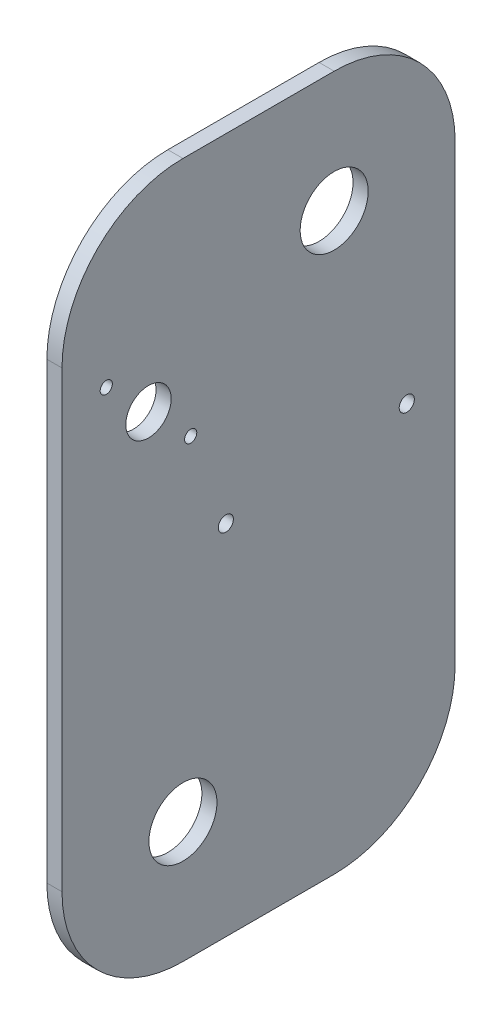
SolidWorks part; units mm, degrees
ref_plane "Front Plane" through (0, 0, 0) normal (0, 0, 1) x (1, 0, 0)
ref_plane "Top Plane" through (0, 0, 0) normal (0, 1, 0) x (1, 0, 0)
ref_plane "Right Plane" through (0, 0, 0) normal (1, 0, 0) x (0, 0, -1)
sketch "Sketch1" plane through (0, 0, 0) normal (1, 0, 0) x (0, 0, -1)
  line L1 (-82.55, -146.05) -> (82.55, -146.05)
  line L2 (-82.55, -146.05) -> (-82.55, 146.05)
  line L3 (-82.55, 146.05) -> (82.55, 146.05)
  line L4 (82.55, -146.05) -> (82.55, 146.05)
  line L5 (-82.55, -146.05) -> (82.55, 146.05) construction
  line L6 (-82.55, 146.05) -> (82.55, -146.05) construction
  point P0 (0, 0)
  dimension "D1" = 292.1
  dimension "D2" = 165.1
extrude "Boss-Extrude1" add sketch "Sketch1" along normal mid plane 6.35
fillet "Fillet1" radius 50.8 4 edges at (0, -146.05, -82.55) (0, 146.05, -82.55) (0, 146.05, 82.55) (0, -146.05, 82.55)
sketch "Sketch2" plane through (-3.175, 0, 0) normal (-1, 0, 0) x (0, 0, 1)
  line L0 (82.55, 95.25) -> (82.55, -95.25) construction
  line L1 (31.75, -146.05) -> (-31.75, -146.05) construction
  circle A0 centre (31.75, -95.25) radius 14.2875
  circle A1 centre (-31.75, 95.25) radius 14.2875
  dimension "D1" = 28.575
  dimension "D2" = 50.8
  dimension "D3" = 50.8
  dimension "D4" = 28.575
  dimension "D5" = 190.5
  dimension "D6" = 63.5
extrude "Cut-Extrude1" cut sketch "Sketch2" against normal through all
sketch "Sketch4" plane through (3.175, 0, 0) normal (1, 0, 0) x (0, 0, -1)
  circle A1 centre (62.2418, 9.9114) radius 3.175
  circle A2 centre (62.2418, 9.9114) radius 3.175
  circle A3 centre (-13.7505, 4.2889) radius 3.175
  circle A4 centre (-13.7505, 4.2889) radius 3.175
  dimension "D1" = 0
  dimension "D2" = 0
extrude "Cut-Extrude3" cut sketch "Sketch4" against normal through all
sketch "Sketch5" plane through (-3.175, 0, 0) normal (-1, 0, 0) x (0, 0, 1)
  line L0 (-21.3786, 120.2396) -> (57.2116, 87.6224) construction
  line L1 (-57.4179, 86.694) -> (6.0821, -103.806) construction
  line L2 (74.7279, 58.2331) -> (58.6645, -98.017) construction
  line L3 (-21.3786, 120.2396) -> (-31.75, 95.25) construction
  line L4 (-57.4179, 86.694) -> (-31.75, 95.25) construction
  line L5 (74.7279, 58.2331) -> (46.2302, 61.1628) construction
  line L6 (46.2302, 61.1628) -> (57.2116, 87.6224) construction
  line L7 (6.0821, -103.806) -> (31.75, -95.25) construction
  line L8 (31.75, -95.25) -> (58.6645, -98.017) construction
  line L10 (28.501, 43.4336) -> (63.9594, 43.4336) construction
  line L11 (28.501, 43.4336) -> (28.501, 78.892) construction
  line L12 (28.501, 78.892) -> (63.9594, 78.892) construction
  line L13 (63.9594, 43.4336) -> (63.9594, 78.892) construction
  line L14 (28.501, 43.4336) -> (63.9594, 78.892) construction
  line L15 (28.501, 78.892) -> (63.9594, 43.4336) construction
  circle A0 centre (46.2302, 61.1628) radius 9.525
  circle A1 centre (63.9594, 78.892) radius 2.5527
  circle A2 centre (-31.75, 95.25) radius 27.0563 construction
  circle A3 centre (46.2302, 61.1628) radius 28.6479 construction
  circle A4 centre (31.75, -95.25) radius 27.0563 construction
  circle A5 centre (28.501, 43.4336) radius 2.5527
  dimension "D1" = 19.05
  dimension "D2" = 54.1127
  dimension "D3" = 57.2958
  dimension "D4" = 54.1127
  dimension "D9" = 5.1054
  dimension "D6" = 85.09
  dimension "D7" = 200.8046
  dimension "D5" = 73.33
  dimension "D10" = 35.4584
  dimension "D11" = 130.975
  dimension "D12" = 155.695
  dimension "D8" = 157.0736
extrude "Cut-Extrude4" cut sketch "Sketch5" against normal through all
equation "\"D3@Sketch5\"=36*5mm/PI"
equation "\"D4@Sketch5\"=\"D2@Sketch5\""
equation "\"D2@Sketch5\"=34*5mm/PI"
equation "\"circ 34t a\"= PI * \"D2@Sketch5\" * \"D11@Sketch5\" / 360"
equation "\"circ 36t\"= PI * \"D3@Sketch5\" * \"D5@Sketch5\" / 360"
equation "\"circ 34t b\"= PI * \"D4@Sketch5\" * \"D12@Sketch5\" / 360"
equation "\"total circ\"= \"circ 34t a\" + \"circ 34t b\" + \"circ 36t\""
equation "\"total straight\"= \"D7@Sketch5\" + \"D6@Sketch5\" + \"D8@Sketch5\""
equation "\"belt length\"= 615mm"
equation "\"total belt\"= \"total straight\" + \"total circ\""
